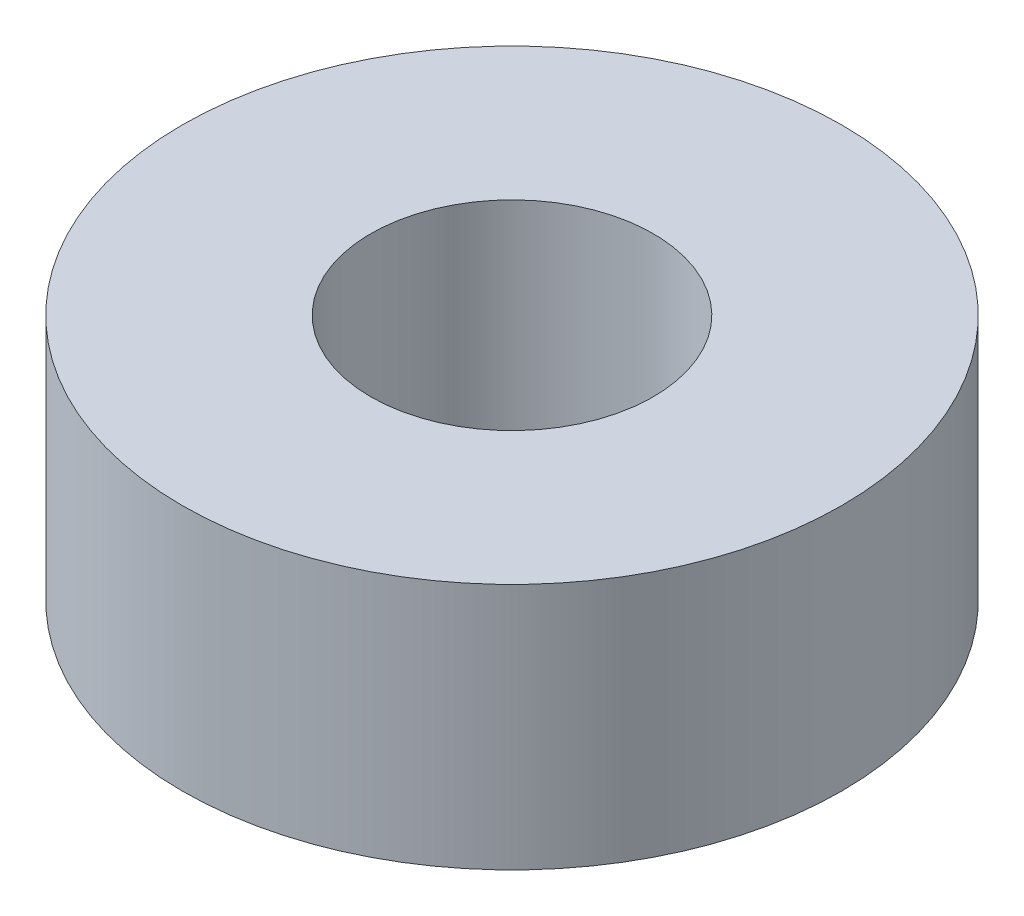
SolidWorks part; units mm, degrees
ref_plane "Front" through (0, 0, 0) normal (0, 0, 1) x (1, 0, 0)
ref_plane "Top" through (0, 0, 0) normal (0, 1, 0) x (1, 0, 0)
ref_plane "Right" through (0, 0, 0) normal (1, 0, 0) x (0, 0, -1)
sketch "Sketch1" plane through (0, 0, 0) normal (0, 1, 0) x (1, 0, 0)
  circle A0 centre (0, 0) radius 4
  circle A1 centre (0, 0) radius 1.7145
  dimension "D1" = 3.429
  dimension "D2" = 8
extrude "Boss-Extrude1" add sketch "Sketch1" along normal blind 3
